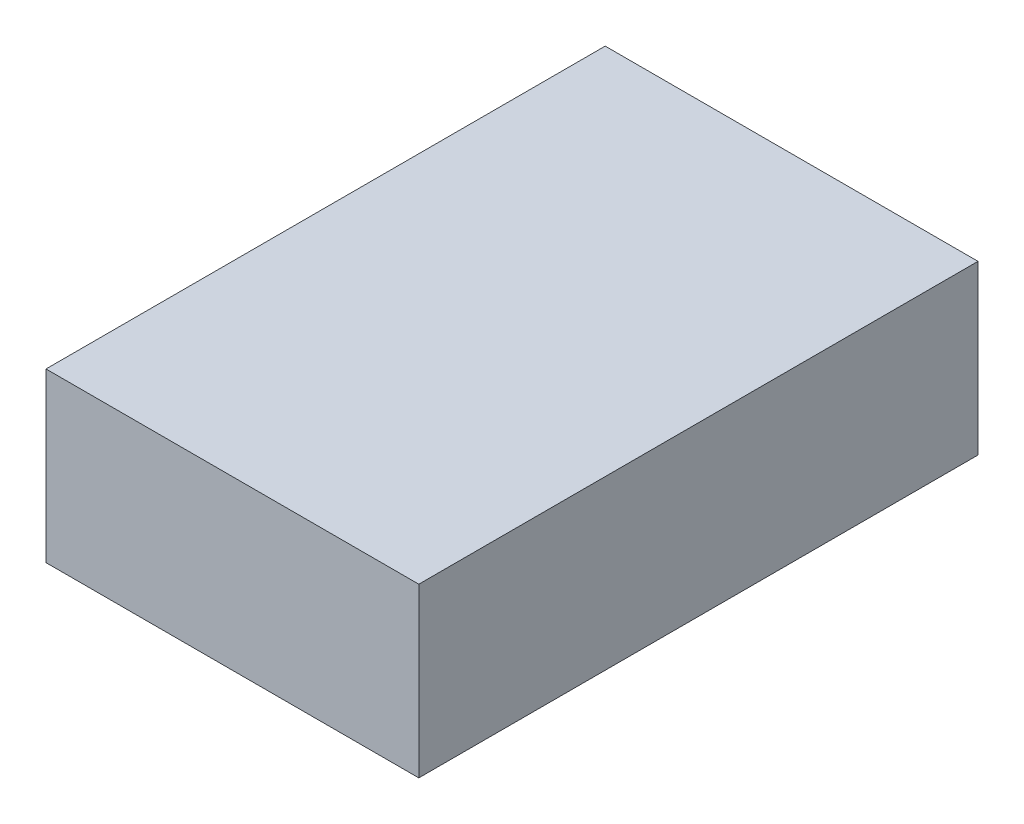
SolidWorks part; units mm, degrees
ref_plane "Front Plane" through (0, 0, 0) normal (0, 0, 1) x (1, 0, 0)
ref_plane "Top Plane" through (0, 0, 0) normal (0, 1, 0) x (1, 0, 0)
ref_plane "Right Plane" through (0, 0, 0) normal (1, 0, 0) x (0, 0, -1)
sketch "Sketch1" plane through (0, 0, 0) normal (0, 1, 0) x (1, 0, 0)
  line L1 (-1, 1.5) -> (1, 1.5)
  line L2 (-1, 1.5) -> (-1, -1.5)
  line L3 (-1, -1.5) -> (1, -1.5)
  line L4 (1, 1.5) -> (1, -1.5)
  line L5 (-1, 1.5) -> (1, -1.5) construction
  line L6 (-1, -1.5) -> (1, 1.5) construction
  point P0 (0, 0)
  dimension "D1" = 2
  dimension "D2" = 3
extrude "Boss-Extrude1" add sketch "Sketch1" along normal blind 0.9
